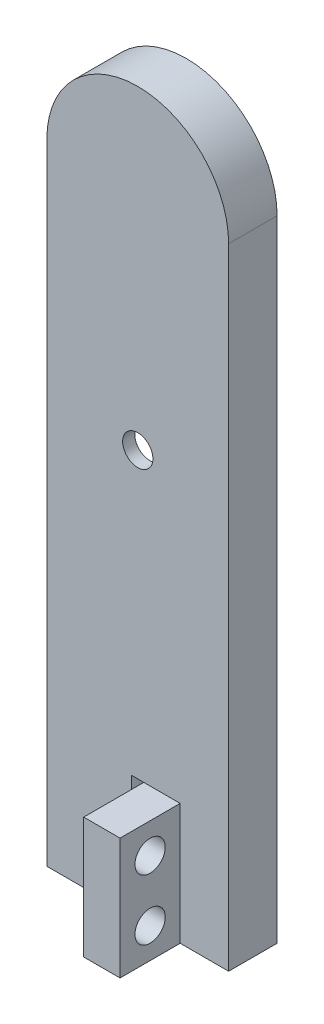
SolidWorks part; units mm, degrees
ref_plane "前基準面" through (0, 0, 0) normal (0, 0, 1) x (1, 0, 0)
ref_plane "上基準面" through (0, 0, 0) normal (0, 1, 0) x (1, 0, 0)
ref_plane "右基準面" through (0, 0, 0) normal (1, 0, 0) x (0, 0, -1)
sketch "草圖1" plane through (0, 0, 0) normal (0, 0, 1) x (1, 0, 0)
  line L0 (0, 0) -> (0, 4.6483) construction
  line L1 (7.5, 0) -> (7.5, 52)
  line L2 (7.5, 0) -> (-7.5, 0)
  line L3 (-7.5, 0) -> (-7.5, 52)
  arc A0 (7.5, 52) -> (-7.5, 52) centre (0, 52) ccw
  dimension "D1" = 7.5
  dimension "D2" = 52
extrude "填料-伸長1" add sketch "草圖1" along normal blind 4
sketch "草圖3" plane through (0, 0, 0) normal (0, 0, 1) x (1, 0, 0)
  line L0 (0, 0) -> (0, 14.6981) construction
  line L1 (7.5, 52) -> (-7.5, 52) construction
  line L2 (7.5, 15) -> (-7.5, 15) construction
  line L3 (7.5, 0) -> (7.5, 52) construction
  line L4 (-7.5, 52) -> (-7.5, 0) construction
  line L5 (-7.5, 0) -> (7.5, 0) construction
  line L6 (7.5, 33.5) -> (5, 33.5) construction
  line L7 (5, 33.5) -> (2.2723, 16.6325)
  line L8 (5, 33.5) -> (2.2966, 50)
  line L9 (-2.2966, 50) -> (-5, 33.5)
  line L10 (-5, 33.5) -> (-2.3019, 17)
  line L11 (0, 52.2966) -> (0, 59.5) construction
  line L12 (-5, 33.5) -> (-7.5, 33.5) construction
  arc A0 (7.5, 52) -> (-7.5, 52) centre (0, 52) ccw construction
  arc A1 (-4.7386, 35.0956) -> (-4.7396, 31.9073) centre (0, 33.5) ccw
  arc A2 (-2.3019, 17) -> (2.2723, 16.6325) centre (0, 17) ccw
  arc A3 (-2.2966, 50) -> (2.2966, 50) centre (0, 50) cw
  arc A4 (4.7452, 31.9241) -> (4.7386, 35.0956) centre (0, 33.5) ccw
  dimension "D4" = 10
  dimension "D5" = 16.5
  dimension "D1" = 15
  dimension "D2" = 37
  dimension "D3" = 18.5
extrude "除料-伸長1" cut sketch "草圖3" along normal blind 3 contours A3 L9 L10 A2 L7 L8
sketch "草圖5" plane through (0, 0, 0) normal (0, 0, 1) x (1, 0, 0)
  line L0 (5, 33.5) -> (-5, 33.5) construction
  circle A0 centre (0, 33.5) radius 1.25
  dimension "D1" = 2.5
extrude "除料-伸長2" cut sketch "草圖5" along normal blind 12.4
sketch "草圖6" plane through (0, 0, 0) normal (0, 0, 1) x (1, 0, 0)
  line L0 (0, 0) -> (0, 56.6939) construction
  line L1 (0.5, 0) -> (0.5, 10)
  line L2 (7.5, 0) -> (-7.5, 0) construction
  line L3 (0.5, 10) -> (-0.5, 10)
  line L4 (0.5, 0) -> (-0.5, 0)
  line L5 (-0.5, 0) -> (-0.5, 10)
  point P10 (0, 10)
  dimension "D1" = 0.5
  dimension "D2" = 10
extrude "除料-伸長3" cut sketch "草圖6" along normal blind 16.3
ref_plane "平面1" through (0.5, 0, 0) normal (1, 0, 0) x (0, 0, -1)
sketch "草圖9" plane through (0.5, 0, 0) normal (1, 0, 0) x (0, 0, -1)
  line L0 (-4, 0) -> (0, 0) construction
  line L1 (-8.9618, 10) -> (-3.9618, 10)
  line L2 (-8.9618, 10) -> (-8.9618, 0)
  line L3 (-8.9618, 0) -> (-3.9618, 0)
  line L4 (-3.9618, 10) -> (-3.9618, 0)
  dimension "D1" = 5
  dimension "D2" = 10
extrude "填料-伸長4" add sketch "草圖9" along normal blind 3
sketch "草圖10" plane through (0.5, 0, 0) normal (1, 0, 0) x (0, 0, -1)
  line L0 (-8.9618, 5) -> (-4, 5) construction
  line L1 (-8.9618, 10) -> (-8.9618, 0) construction
  line L2 (-4, 0) -> (-4, 10) construction
  line L3 (-6.4809, 10) -> (-6.4809, 0) construction
  line L4 (-4, 10) -> (-8.9618, 10) construction
  line L5 (-8.9618, 0) -> (-4, 0) construction
  circle A0 centre (-6.4809, 7.5) radius 1.25
  circle A1 centre (-6.4809, 2.5) radius 1.25
  dimension "D2" = 2.5
  dimension "D1" = 2.5
extrude "除料-伸長4" cut sketch "草圖10" along normal blind 5.1
